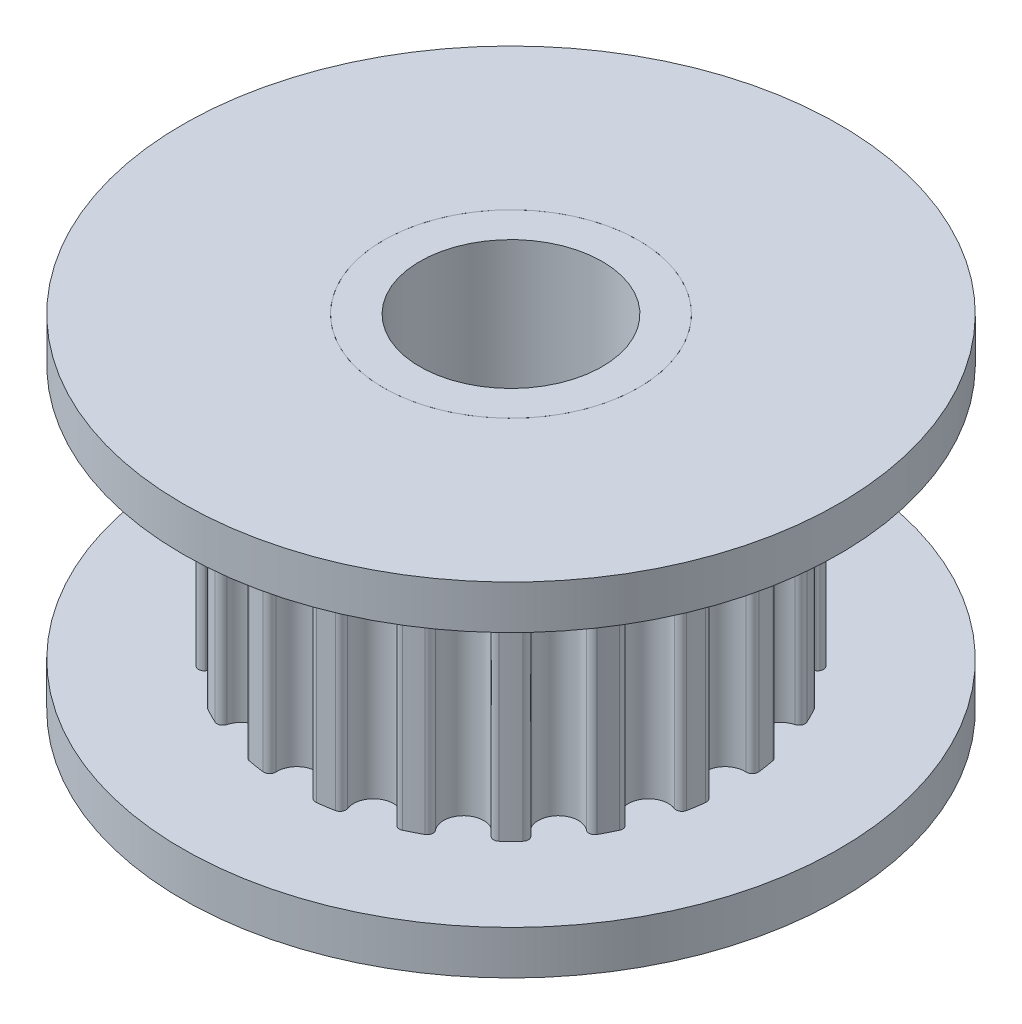
SolidWorks part; units mm, degrees
ref_plane "Přední rovina" through (0, 0, 0) normal (0, 0, 1) x (1, 0, 0)
ref_plane "Horní rovina" through (0, 0, 0) normal (0, 1, 0) x (1, 0, 0)
ref_plane "Pravá rovina" through (0, 0, 0) normal (1, 0, 0) x (0, 0, -1)
sketch "Skica2" plane through (0, 0, 0) normal (0, 0, 1) x (1, 0, 0)
  line L0 (3.5, 9.4) -> (2.5, 9.4)
  line L1 (2.5, 9.4) -> (2.5, 0)
  line L2 (2.5, 0) -> (3.5, 0)
  line L3 (0, 0) -> (0, 9.4) construction
  line L4 (0, 9.4) -> (2.5, 9.4)
  line L5 (0, 0) -> (2.5, 0)
  line L6 (3.5, 0) -> (3.5, 1.2)
  line L9 (7.5, 8.2) -> (3.5, 8.2)
  line L12 (7.5, 1.2) -> (3.5, 1.2)
  line L13 (3.5, 8.2) -> (3.5, 9.4)
  line L14 (7.5, 1.2) -> (7.5, 8.2)
  dimension "D3" = 7
  dimension "D1" = 1
  dimension "D2" = 1.2
  dimension "D4" = 4
  dimension "D5" = 1.2
  dimension "D6" = 7.5
revolve "Rotovat1" add sketch "Skica2" angle 360 about L3
sketch "Skica3" plane through (0, 9.4, 0) normal (0, 1, 0) x (1, 0, 0)
  circle A0 centre (0, 0) radius 9
  circle A1 centre (0, 0) radius 3.5
  dimension "D1" = 18
  dimension "D2" = 7
extrude "Přidat vysunutím1" add sketch "Skica3" against normal blind 1.2 separate body
sketch "Skica5" plane through (0, 1.2, 0) normal (0, -1, 0) x (1, 0, 0)
  arc A1 (-0.5492, 5.8991) -> (0.5492, 5.8991) centre (0, 5.87) ccw
  arc A2 (-0.5492, 5.8991) -> (-0.7281, 6.0665) centre (-0.709, 5.9076) ccw
  arc A3 (0.7281, 6.0665) -> (0.5492, 5.8991) centre (0.709, 5.9076) ccw
  arc A4 (1.1822, 5.9945) -> (0.7281, 6.0665) centre (0, 0) ccw
  arc A5 (1.3006, 5.7801) -> (2.3453, 5.4407) centre (1.8139, 5.5827) ccw
  arc A6 (1.3006, 5.7801) -> (1.1822, 5.9945) centre (1.1512, 5.8376) ccw
  arc A7 (2.5671, 5.5446) -> (2.3453, 5.4407) centre (2.4999, 5.3994) ccw
  arc A8 (2.9768, 5.3358) -> (2.5671, 5.5446) centre (0, 0) ccw
  arc A9 (3.0231, 5.0953) -> (3.9118, 4.4497) centre (3.4503, 4.7489) ccw
  arc A10 (3.0231, 5.0953) -> (2.9768, 5.3358) centre (2.8988, 5.1961) ccw
  arc A11 (4.1548, 4.4799) -> (3.9118, 4.4497) centre (4.046, 4.3626) ccw
  arc A12 (4.4799, 4.1548) -> (4.1548, 4.4799) centre (0, 0) ccw
  arc A13 (4.4497, 3.9118) -> (5.0953, 3.0231) centre (4.7489, 3.4503) ccw
  arc A14 (4.4497, 3.9118) -> (4.4799, 4.1548) centre (4.3626, 4.046) ccw
  arc A15 (5.3358, 2.9768) -> (5.0953, 3.0231) centre (5.1961, 2.8988) ccw
  arc A16 (5.5446, 2.5671) -> (5.3358, 2.9768) centre (0, 0) ccw
  arc A17 (5.4407, 2.3453) -> (5.7801, 1.3006) centre (5.5827, 1.8139) ccw
  arc A18 (5.4407, 2.3453) -> (5.5446, 2.5671) centre (5.3994, 2.4999) ccw
  arc A19 (5.9945, 1.1822) -> (5.7801, 1.3006) centre (5.8376, 1.1512) ccw
  arc A20 (6.0665, 0.7281) -> (5.9945, 1.1822) centre (0, 0) ccw
  arc A21 (5.8991, 0.5492) -> (5.8991, -0.5492) centre (5.87, 0) ccw
  arc A22 (5.8991, 0.5492) -> (6.0665, 0.7281) centre (5.9076, 0.709) ccw
  arc A23 (6.0665, -0.7281) -> (5.8991, -0.5492) centre (5.9076, -0.709) ccw
  arc A24 (5.9945, -1.1822) -> (6.0665, -0.7281) centre (0, 0) ccw
  arc A25 (5.7801, -1.3006) -> (5.4407, -2.3453) centre (5.5827, -1.8139) ccw
  arc A26 (5.7801, -1.3006) -> (5.9945, -1.1822) centre (5.8376, -1.1512) ccw
  arc A27 (5.5446, -2.5671) -> (5.4407, -2.3453) centre (5.3994, -2.4999) ccw
  arc A28 (5.3358, -2.9768) -> (5.5446, -2.5671) centre (0, 0) ccw
  arc A29 (5.0953, -3.0231) -> (4.4497, -3.9118) centre (4.7489, -3.4503) ccw
  arc A30 (5.0953, -3.0231) -> (5.3358, -2.9768) centre (5.1961, -2.8988) ccw
  arc A31 (4.4799, -4.1548) -> (4.4497, -3.9118) centre (4.3626, -4.046) ccw
  arc A32 (4.1548, -4.4799) -> (4.4799, -4.1548) centre (0, 0) ccw
  arc A33 (3.9118, -4.4497) -> (3.0231, -5.0953) centre (3.4503, -4.7489) ccw
  arc A34 (3.9118, -4.4497) -> (4.1548, -4.4799) centre (4.046, -4.3626) ccw
  arc A35 (2.9768, -5.3358) -> (3.0231, -5.0953) centre (2.8988, -5.1961) ccw
  arc A36 (2.5671, -5.5446) -> (2.9768, -5.3358) centre (0, 0) ccw
  arc A37 (2.3453, -5.4407) -> (1.3006, -5.7801) centre (1.8139, -5.5827) ccw
  arc A38 (2.3453, -5.4407) -> (2.5671, -5.5446) centre (2.4999, -5.3994) ccw
  arc A39 (1.1822, -5.9945) -> (1.3006, -5.7801) centre (1.1512, -5.8376) ccw
  arc A40 (0.7281, -6.0665) -> (1.1822, -5.9945) centre (0, 0) ccw
  arc A41 (0.5492, -5.8991) -> (-0.5492, -5.8991) centre (0, -5.87) ccw
  arc A42 (0.5492, -5.8991) -> (0.7281, -6.0665) centre (0.709, -5.9076) ccw
  arc A43 (-0.7281, -6.0665) -> (-0.5492, -5.8991) centre (-0.709, -5.9076) ccw
  arc A44 (-1.1822, -5.9945) -> (-0.7281, -6.0665) centre (0, 0) ccw
  arc A45 (-1.3006, -5.7801) -> (-2.3453, -5.4407) centre (-1.8139, -5.5827) ccw
  arc A46 (-1.3006, -5.7801) -> (-1.1822, -5.9945) centre (-1.1512, -5.8376) ccw
  arc A47 (-2.5671, -5.5446) -> (-2.3453, -5.4407) centre (-2.4999, -5.3994) ccw
  arc A48 (-2.9768, -5.3358) -> (-2.5671, -5.5446) centre (0, 0) ccw
  arc A49 (-3.0231, -5.0953) -> (-3.9118, -4.4497) centre (-3.4503, -4.7489) ccw
  arc A50 (-3.0231, -5.0953) -> (-2.9768, -5.3358) centre (-2.8988, -5.1961) ccw
  arc A51 (-4.1548, -4.4799) -> (-3.9118, -4.4497) centre (-4.046, -4.3626) ccw
  arc A52 (-4.4799, -4.1548) -> (-4.1548, -4.4799) centre (0, 0) ccw
  arc A53 (-4.4497, -3.9118) -> (-5.0953, -3.0231) centre (-4.7489, -3.4503) ccw
  arc A54 (-4.4497, -3.9118) -> (-4.4799, -4.1548) centre (-4.3626, -4.046) ccw
  arc A55 (-5.3358, -2.9768) -> (-5.0953, -3.0231) centre (-5.1961, -2.8988) ccw
  arc A56 (-5.5446, -2.5671) -> (-5.3358, -2.9768) centre (0, 0) ccw
  arc A57 (-5.4407, -2.3453) -> (-5.7801, -1.3006) centre (-5.5827, -1.8139) ccw
  arc A58 (-5.4407, -2.3453) -> (-5.5446, -2.5671) centre (-5.3994, -2.4999) ccw
  arc A59 (-5.9945, -1.1822) -> (-5.7801, -1.3006) centre (-5.8376, -1.1512) ccw
  arc A60 (-6.0665, -0.7281) -> (-5.9945, -1.1822) centre (0, 0) ccw
  arc A61 (-5.8991, -0.5492) -> (-5.8991, 0.5492) centre (-5.87, 0) ccw
  arc A62 (-5.8991, -0.5492) -> (-6.0665, -0.7281) centre (-5.9076, -0.709) ccw
  arc A63 (-6.0665, 0.7281) -> (-5.8991, 0.5492) centre (-5.9076, 0.709) ccw
  arc A64 (-5.9945, 1.1822) -> (-6.0665, 0.7281) centre (0, 0) ccw
  arc A65 (-5.7801, 1.3006) -> (-5.4407, 2.3453) centre (-5.5827, 1.8139) ccw
  arc A66 (-5.7801, 1.3006) -> (-5.9945, 1.1822) centre (-5.8376, 1.1512) ccw
  arc A67 (-5.5446, 2.5671) -> (-5.4407, 2.3453) centre (-5.3994, 2.4999) ccw
  arc A68 (-5.3358, 2.9768) -> (-5.5446, 2.5671) centre (0, 0) ccw
  arc A69 (-5.0953, 3.0231) -> (-4.4497, 3.9118) centre (-4.7489, 3.4503) ccw
  arc A70 (-5.0953, 3.0231) -> (-5.3358, 2.9768) centre (-5.1961, 2.8988) ccw
  arc A71 (-4.4799, 4.1548) -> (-4.4497, 3.9118) centre (-4.3626, 4.046) ccw
  arc A72 (-4.1548, 4.4799) -> (-4.4799, 4.1548) centre (0, 0) ccw
  arc A73 (-3.9118, 4.4497) -> (-3.0231, 5.0953) centre (-3.4503, 4.7489) ccw
  arc A74 (-3.9118, 4.4497) -> (-4.1548, 4.4799) centre (-4.046, 4.3626) ccw
  arc A75 (-2.9768, 5.3358) -> (-3.0231, 5.0953) centre (-2.8988, 5.1961) ccw
  arc A76 (-2.5671, 5.5446) -> (-2.9768, 5.3358) centre (0, 0) ccw
  arc A77 (-2.3453, 5.4407) -> (-1.3006, 5.7801) centre (-1.8139, 5.5827) ccw
  arc A78 (-2.3453, 5.4407) -> (-2.5671, 5.5446) centre (-2.4999, 5.3994) ccw
  arc A79 (-1.1822, 5.9945) -> (-1.3006, 5.7801) centre (-1.1512, 5.8376) ccw
  arc A80 (-0.7281, 6.0665) -> (-1.1822, 5.9945) centre (0, 0) ccw
  circle A81 centre (0, 0) radius 7.5
  point P4 (0, 0)
  point P144 (0, 0)
extrude "Odebrat vysunutím1" cut sketch "Skica5" against normal blind 7
sketch "Skica6" plane through (0, 1.2, 0) normal (0, -1, 0) x (1, 0, 0)
  circle A0 centre (0, 0) radius 3.5
  circle A1 centre (0, 0) radius 9
  circle A2 centre (0, 0) radius 9 construction
extrude "Přidat vysunutím3" add sketch "Skica6" along normal blind 1.2 separate body
